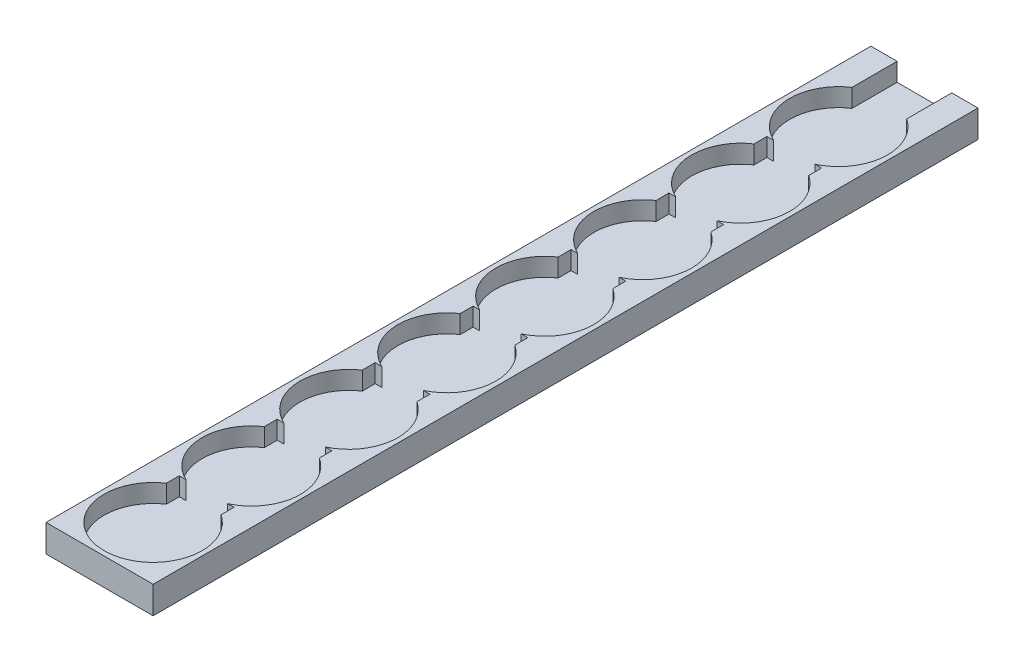
SolidWorks part; units mm, degrees
ref_plane "Front Plane" through (0, 0, 0) normal (0, 0, 1) x (1, 0, 0)
ref_plane "Top Plane" through (0, 0, 0) normal (0, 1, 0) x (1, 0, 0)
ref_plane "Right Plane" through (0, 0, 0) normal (1, 0, 0) x (0, 0, -1)
sketch "Sketch1" plane through (0, 0, 0) normal (0, 1, 0) x (1, 0, 0)
  line L1 (0, 0) -> (23.5, 0)
  line L2 (0, 0) -> (0, 181)
  line L3 (0, 181) -> (23.5, 181)
  line L4 (23.5, 0) -> (23.5, 181)
  dimension "D1" = 23.5
  dimension "D2" = 181
extrude "Boss-Extrude1" add sketch "Sketch1" against normal blind 6
sketch "Sketch2" plane through (0, 0, 0) normal (0, 1, 0) x (1, 0, 0)
  line L0 (23.5, 0) -> (23.5, 181) construction
  line L1 (0, 0) -> (23.5, 0) construction
  circle A0 centre (11.75, 11.75) radius 10.75
  dimension "D1" = 21.5
  dimension "D2" = 11.75
  dimension "D3" = 11.75
extrude "Cut-Extrude1" cut sketch "Sketch2" against normal blind 4
sketch "Sketch3" plane through (0, 0, 0) normal (0, 1, 0) x (1, 0, 0)
  line L0 (23.5, 0) -> (23.5, 181) construction
  line L1 (5.75, 23.5) -> (17.75, 23.5)
  line L2 (5.75, 23.5) -> (5.75, 20.6698)
  line L3 (5.75, 20.6698) -> (17.75, 20.6698)
  line L4 (17.75, 23.5) -> (17.75, 20.6698)
  circle A0 centre (11.75, 11.75) radius 10.75 construction
  circle A2 centre (11.75, 11.75) radius 10.75 construction
  point P8 (17.995, 22.7765)
  point P11 (11.75, 11.75)
  dimension "D1" = 12
  dimension "D2" = 11.75
  dimension "D4" = 5.75
extrude "Cut-Extrude2" cut sketch "Sketch3" against normal blind 4
sketch "Sketch5" plane through (0, 0, 0) normal (0, 1, 0) x (1, 0, 0)
  circle A0 centre (11.8453, 33.25) radius 10.75
  circle A1 centre (11.75, 11.75) radius 10.75 construction
  dimension "D1" = 21.5
  dimension "D2" = 21.5
extrude "Cut-Extrude5" cut sketch "Sketch5" against normal blind 4
pattern_linear "LPattern1" count 8 spacing 21.49 along (0, 0, -1) of "Cut-Extrude2", "Cut-Extrude1"
sketch "Sketch4" plane through (0, 0, -173.93) normal (0, 0, 1) x (1, 0, 0)
  line L0 (17.75, -4) -> (17.75, 0) construction
  line L1 (5.75, 0) -> (17.75, 0)
  line L2 (5.75, 0) -> (5.75, -4)
  line L3 (5.75, -4) -> (17.75, -4)
  line L4 (17.75, 0) -> (17.75, -4)
  line L5 (17.75, -4) -> (5.75, -4) construction
extrude "Cut-Extrude3" cut sketch "Sketch4" against normal through all
